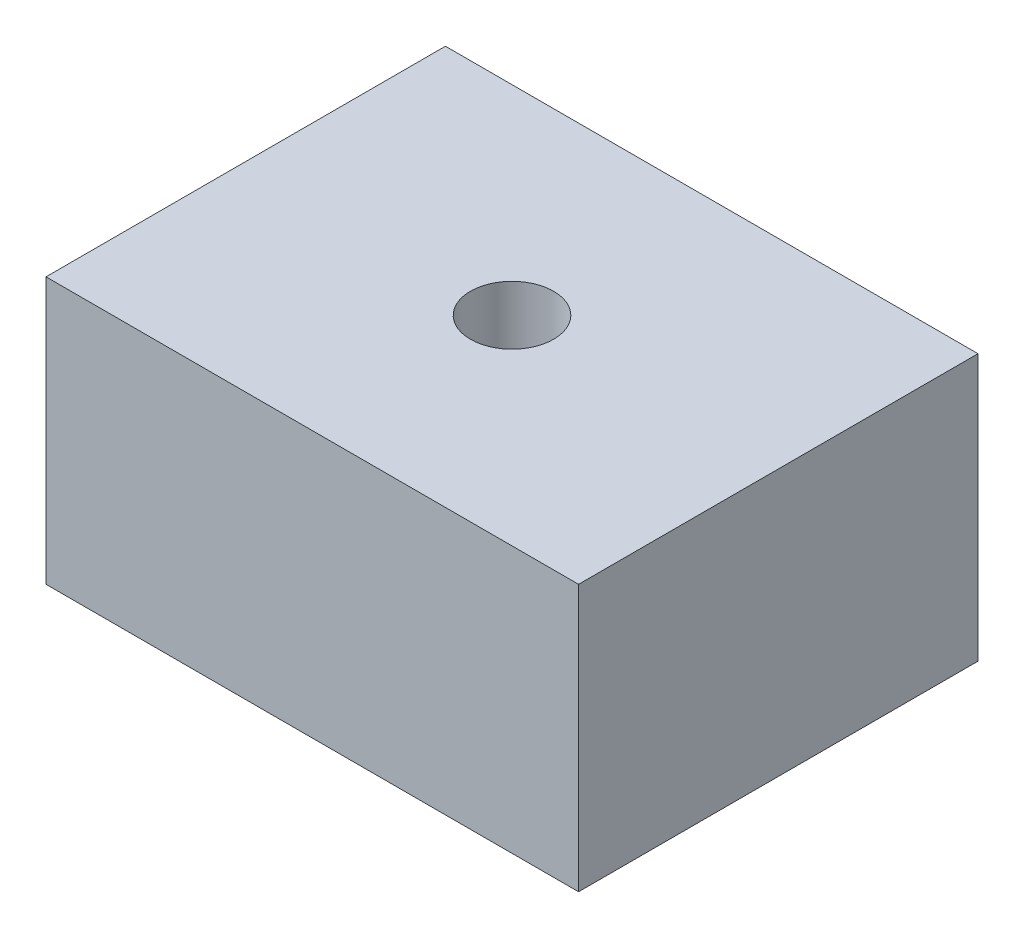
SolidWorks part; units mm, degrees
ref_plane "Front Plane" through (0, 0, 0) normal (0, 0, 1) x (1, 0, 0)
ref_plane "Top Plane" through (0, 0, 0) normal (0, 1, 0) x (1, 0, 0)
ref_plane "Right Plane" through (0, 0, 0) normal (1, 0, 0) x (0, 0, -1)
sketch "Sketch1" plane through (0, 0, 0) normal (0, 1, 0) x (1, 0, 0)
  line L1 (0, 0) -> (50.8, 0)
  line L2 (0, 0) -> (0, -38.1)
  line L3 (0, -38.1) -> (50.8, -38.1)
  line L4 (50.8, 0) -> (50.8, -38.1)
  dimension "D1" = 38.1
  dimension "D2" = 50.8
extrude "Boss-Extrude1" add sketch "Sketch1" along normal blind 25.4
hole_wizard "3/8-16 Tapped Hole1" positions "Sketch2" profile "Sketch3" tap size "3/8-16" standard "ANSI Inch" end condition through all
sketch "Sketch2" plane through (0, 25.4, 0) normal (0, 1, 0) x (1, 0, 0)
  line L0 (0, 0) -> (0, -38.1) construction
  line L1 (50.8, 0) -> (0, 0) construction
  point P0 (25.4, -19.05)
  dimension "D1" = 25.4
  dimension "D2" = 19.05
cosmetic thread "Hole Thread1" parameters "D2"=9.525
sketch "Sketch3" plane through (25.4, 25.4, 19.05) normal (1, 0, 0) x (0, 0, 1)
  line L0 (0, 0) -> (0, 25.4)
  line L1 (0, 25.4) -> (3.9687, 25.4)
  line L2 (3.9687, 25.4) -> (3.9687, 0)
  line L5 (3.9687, 0) -> (0, 0)
  line L11 (0, -6.35) -> (0, 107.95) construction
  dimension "Thru Tap Drill Dia." = 7.9375
  dimension "Thru Tap Drill Depth" = 25.4
